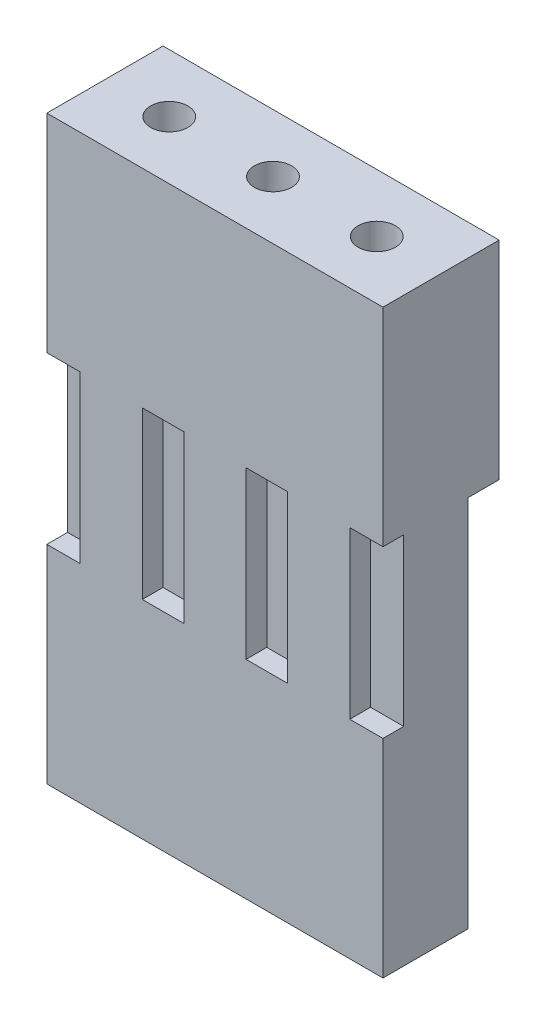
SolidWorks part; units mm, degrees
material "ABS"
ref_plane "Front Plane" through (0, 0, 0) normal (0, 0, 1) x (1, 0, 0)
ref_plane "Top Plane" through (0, 0, 0) normal (0, 1, 0) x (1, 0, 0)
ref_plane "Right Plane" through (0, 0, 0) normal (1, 0, 0) x (0, 0, -1)
sketch "Sketch3" plane through (0, 0, 0) normal (0, 1, 0) x (1, 0, 0)
  line L0 (0, 0) -> (0, 1.4) construction
  line L1 (-4.05, 1.4) -> (4.05, 1.4)
  line L2 (-4.05, 1.4) -> (-4.05, -1.4)
  line L3 (-4.05, -1.4) -> (4.05, -1.4)
  line L4 (4.05, 1.4) -> (4.05, -1.4)
  line L5 (0, 0) -> (4.05, 0) construction
  circle A0 centre (2.5, 0) radius 0.45
  circle A1 centre (-2.5, 0) radius 0.45
  circle A2 centre (0, 0) radius 0.45
  dimension "D3" = 0.9
  dimension "D4" = 5
  dimension "D1" = 8.1
  dimension "D2" = 2.8
extrude "Boss-Extrude1" add sketch "Sketch3" against normal blind 5
sketch "Sketch4" plane through (0, -5, 0) normal (0, -1, 0) x (1, 0, 0)
  line L0 (0, 0) -> (0, 3.536) construction
  line L1 (4.05, -0.65) -> (3.3, -1.4)
  line L2 (-4.05, -0.65) -> (-3.3, -1.4)
  line L4 (-4.05, 1.4) -> (-4.05, -1.4)
  line L5 (-4.05, -1.4) -> (4.05, -1.4)
  line L6 (4.05, -1.4) -> (4.05, 1.4)
  line L7 (4.05, 1.4) -> (-4.05, 1.4)
  line L8 (-4.05, 1.4) -> (-4.05, -0.65)
  line L9 (-3.3, -1.4) -> (3.3, -1.4)
  line L10 (4.05, -0.65) -> (4.05, 1.4)
  line L11 (4.05, 1.4) -> (-4.05, 1.4)
  circle A0 centre (2.5, 0) radius 0.45 construction
  circle A2 centre (2.5, 0) radius 0.45
  circle A3 centre (0, 0) radius 0.45 construction
  circle A4 centre (0, 0) radius 0.45
  circle A5 centre (-2.5, 0) radius 0.45 construction
  circle A6 centre (-2.5, 0) radius 0.45
  dimension "D1" = 0
  dimension "D2" = 6.6
  dimension "D3" = 45
extrude "Boss-Extrude4" add sketch "Sketch4" along normal blind 9
sketch "Sketch7" plane through (0, 0, 1.4) normal (0, 0, 1) x (1, 0, 0)
  line L0 (0, 0) -> (0, -28.1447) construction
  line L2 (-3.25, -5) -> (-3.25, -9)
  line L3 (3.25, -5) -> (4.25, -5)
  line L4 (3.25, -5) -> (3.25, -9)
  line L5 (3.25, -9) -> (4.25, -9)
  line L7 (4.25, -5) -> (4.25, -9)
  line L8 (-3.25, -5) -> (-4.25, -5)
  line L9 (-4.25, -5) -> (-4.25, -9)
  line L10 (-3.25, -9) -> (-4.25, -9)
  line L12 (-0.75, -5) -> (-0.75, -9)
  line L13 (0.75, -5) -> (1.75, -5)
  line L14 (0.75, -5) -> (0.75, -9)
  line L15 (0.75, -9) -> (1.75, -9)
  line L16 (1.75, -5) -> (1.75, -9)
  line L17 (-0.75, -5) -> (-1.75, -5)
  line L18 (-1.75, -5) -> (-1.75, -9)
  line L19 (-0.75, -9) -> (-1.75, -9)
  line L20 (3.3, -5) -> (4.05, -5) construction
  line L22 (4.05, -14) -> (-4.05, -14) construction
  dimension "D1" = 1.5
  dimension "D2" = 1.5
  dimension "D3" = 1
  dimension "D4" = 5
extrude "Cut-Extrude2" cut sketch "Sketch7" against normal blind 0.5
